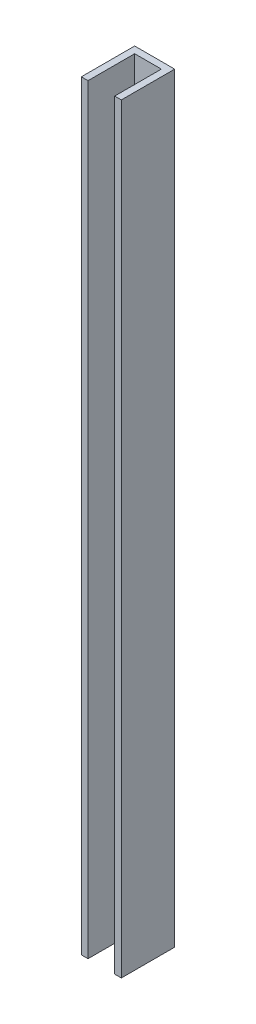
SolidWorks part; units mm, degrees
material "Plain Carbon Steel"
ref_plane "Front Plane" through (0, 0, 0) normal (0, 0, 1) x (1, 0, 0)
ref_plane "Top Plane" through (0, 0, 0) normal (0, 1, 0) x (1, 0, 0)
ref_plane "Right Plane" through (0, 0, 0) normal (1, 0, 0) x (0, 0, -1)
sketch "Sketch1" plane through (0, 0, 0) normal (0, 1, 0) x (1, 0, 0)
  line L0 (0, 0) -> (0, 25.4)
  line L1 (0, 25.4) -> (19.05, 25.4)
  line L2 (19.05, 25.4) -> (19.05, 0)
  line L3 (19.05, 0) -> (15.875, 0)
  line L4 (15.875, 0) -> (15.875, 22.225)
  line L5 (15.875, 22.225) -> (3.175, 22.225)
  line L6 (3.175, 22.225) -> (3.175, 0)
  line L7 (3.175, 0) -> (0, 0)
extrude "Boss-Extrude1" add sketch "Sketch1" along normal blind 361.95
